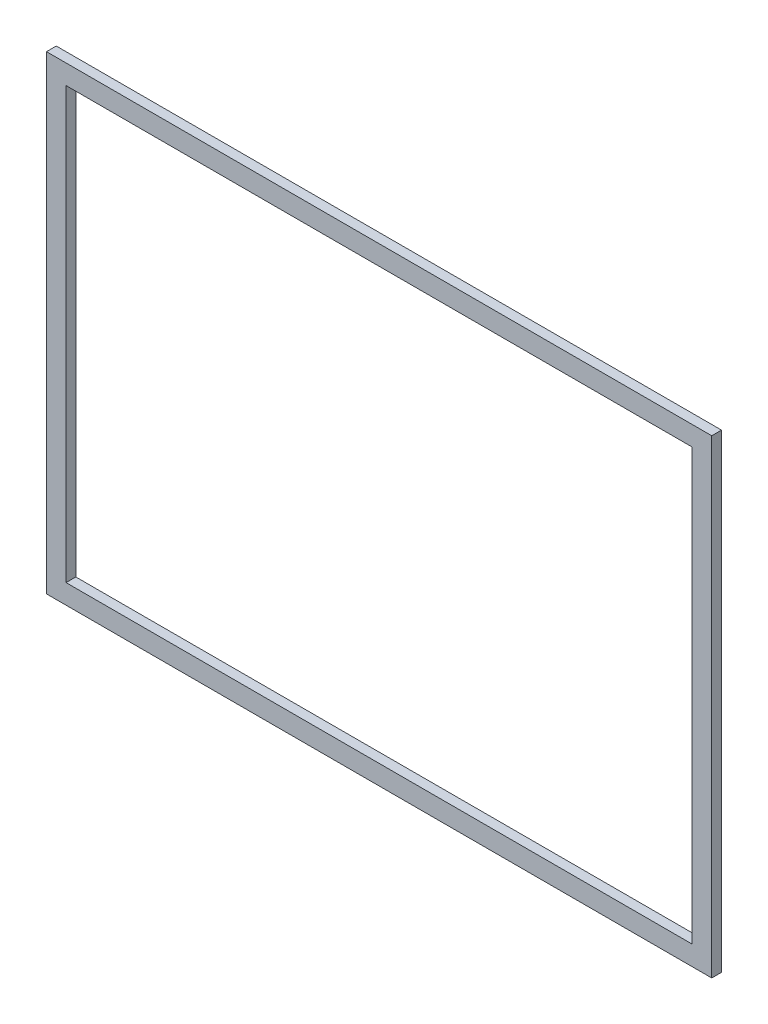
SolidWorks part; units mm, degrees
ref_plane "Plan de face" through (0, 0, 0) normal (0, 0, 1) x (1, 0, 0)
ref_plane "Plan de dessus" through (0, 0, 0) normal (0, 1, 0) x (1, 0, 0)
ref_plane "Plan de droite" through (0, 0, 0) normal (1, 0, 0) x (0, 0, -1)
sketch "Esquisse1" plane through (0, 0, 0) normal (0, 0, 1) x (1, 0, 0)
  line L1 (0, 0) -> (-680, 0)
  line L2 (0, 0) -> (0, 480)
  line L3 (0, 480) -> (-680, 480)
  line L4 (-680, 0) -> (-680, 480)
  line L5 (-660, 460) -> (-20, 460)
  line L6 (-660, 460) -> (-660, 20)
  line L7 (-660, 20) -> (-20, 20)
  line L8 (-20, 460) -> (-20, 20)
  dimension "D1" = 680
  dimension "D2" = 480
  dimension "D3" = 20
  dimension "D4" = 20
  dimension "D5" = 20
  dimension "D6" = 20
extrude "Boss.-Extru.1" add sketch "Esquisse1" along normal blind 10
